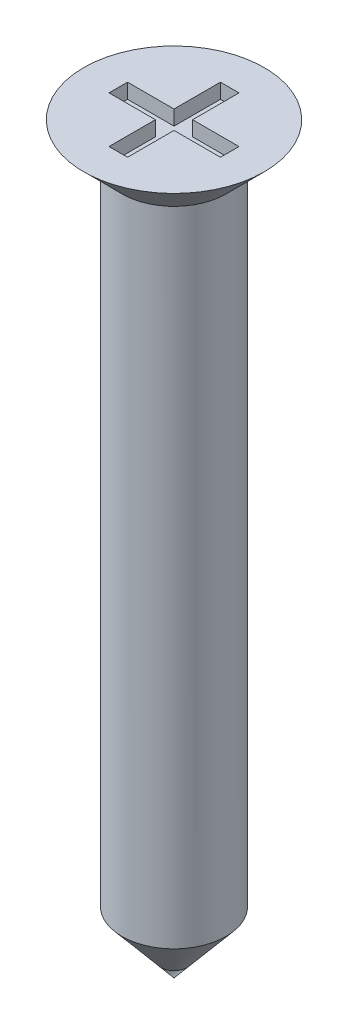
SolidWorks part; units mm, degrees
ref_plane "Front" through (0, 0, 0) normal (0, 0, 1) x (1, 0, 0)
ref_plane "Top" through (0, 0, 0) normal (0, 1, 0) x (1, 0, 0)
ref_plane "Right" through (0, 0, 0) normal (1, 0, 0) x (0, 0, -1)
sketch "Sketch1" plane through (0, 0, 0) normal (0, 0, 1) x (1, 0, 0)
  line L0 (0, 0) -> (-1.215, 0)
  line L1 (-1.215, 0) -> (-0.7, -0.515)
  line L2 (-0.7, -0.515) -> (-0.7, -9.1658)
  line L3 (-0.7, -9.1658) -> (0, -10)
  line L4 (0, -10) -> (0, 0) construction
  line L5 (0, 0) -> (0, -10)
  line L6 (0, -10) -> (-0.7, -10) construction
  dimension "D1" = 2.43
  dimension "D2" = 10
  dimension "D3" = 45
  dimension "D4" = 1.4
  dimension "D5" = 50
revolve "Revolve1" add sketch "Sketch1" angle 360 about L4
sketch "Sketch2" plane through (0, 0, 0) normal (0, 1, 0) x (1, 0, 0)
  line L0 (-0.125, 0.0208) -> (-0.125, 0.125) construction
  line L1 (-0.75, -0.125) -> (-0.125, -0.125)
  line L2 (-0.75, -0.125) -> (-0.75, 0.125)
  line L3 (-0.75, 0.125) -> (-0.125, 0.125)
  line L4 (0.75, -0.125) -> (0.75, 0.125)
  line L5 (-0.75, -0.125) -> (0.75, 0.125) construction
  line L6 (-0.75, 0.125) -> (0.75, -0.125) construction
  line L7 (-0.125, -0.75) -> (0.125, -0.75)
  line L8 (-0.125, -0.75) -> (-0.125, -0.125)
  line L9 (-0.125, 0.75) -> (0.125, 0.75)
  line L10 (0.125, -0.75) -> (0.125, -0.125)
  line L11 (-0.125, -0.75) -> (0, 0) construction
  line L12 (-0.125, 0.75) -> (0.125, -0.75) construction
  line L13 (-0.125, 0.125) -> (-0.125, 0.75)
  line L14 (-0.125, 0.125) -> (-0.0208, 0.125) construction
  line L15 (-0.0208, 0.125) -> (0.0208, 0.125) construction
  line L16 (0.0208, 0.125) -> (0.125, 0.125) construction
  line L17 (0.125, 0.125) -> (0.75, 0.125)
  line L18 (0.125, 0.0208) -> (0.125, 0.125) construction
  line L19 (0.125, 0.125) -> (0.125, 0.75)
  line L20 (0.125, -0.0208) -> (0.125, 0.0208) construction
  line L21 (0.125, -0.125) -> (0.125, -0.0208) construction
  line L22 (0.0208, -0.125) -> (0.125, -0.125) construction
  line L23 (0.125, -0.125) -> (0.75, -0.125)
  line L24 (-0.0208, -0.125) -> (0.0208, -0.125) construction
  line L25 (-0.125, -0.125) -> (-0.0208, -0.125) construction
  line L26 (-0.125, -0.125) -> (-0.125, -0.0208) construction
  line L27 (-0.125, -0.0208) -> (-0.125, 0.0208) construction
  line L28 (0, 0) -> (0.125, 0.75) construction
  point P0 (0, 0)
  point P6 (0, 0)
  dimension "D1" = 0.25
  dimension "D2" = 1.5
extrude "Cut-Extrude1" cut sketch "Sketch2" against normal blind 0.2
